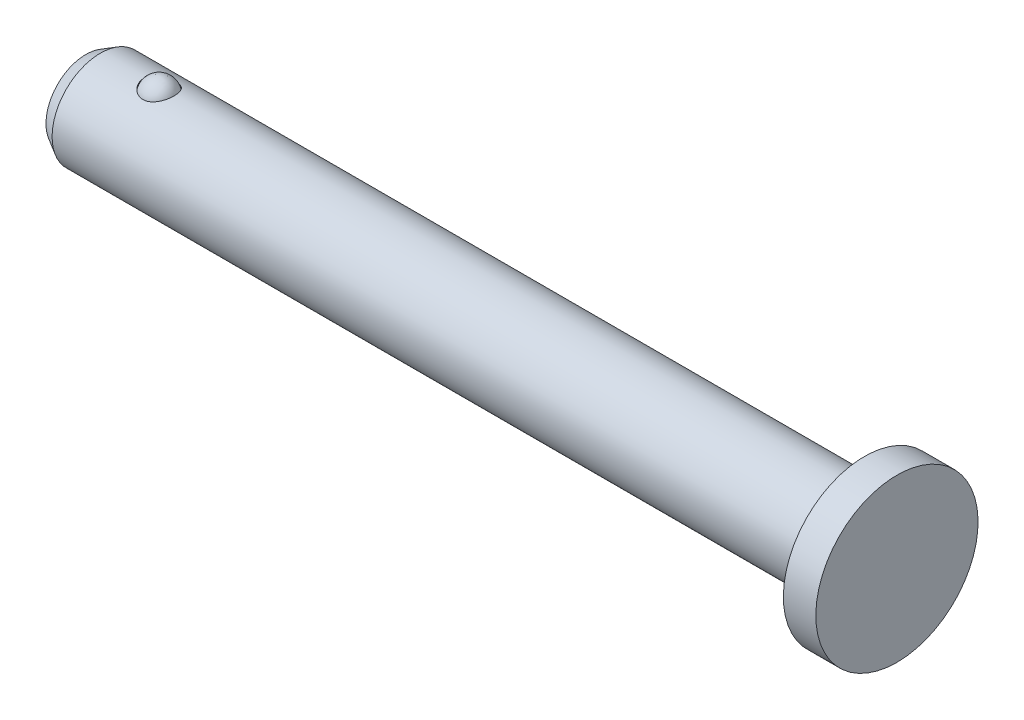
SolidWorks part; units mm, degrees
other "Imported1"
other "Imported2" parameters "D1"=138.0715, "Length"=138.0715, "Usable Length"=107.0085, "Head Height"=13.3603, "Head Diameter"=7.9375, "Diameter"=4.7244, "Shaft Length"=38.1, "Ball Height"=5.1816, "Ball Width"=2.3622, "D2"=54.5332, "F"=55.499, "D10"=11.2649, "D11"=5.3256, "D4"=6.8632, "K"=3.175, "A"=19.0119, "B"=7.112, "D"=21.59, "E"=9.525, "D3"=24.257, "H"=41.275, "D5"=24.257, "Useable Length"=25.4, "D6"=0.9873, "D7"=3.8918, "D8"=4.5254, "D9"=5.5856, "G"=64.77, "D12"=34.036, "C"=6.8932, "A1"=15, "D13"=1.6682, "J"=3.048, "D14"=90, "D15"=34.5361, "Head Dia"=9.525
ref_plane "Front" through (0, 0, 0) normal (0, 0, 1) x (1, 0, 0)
ref_plane "Top" through (0, 0, 0) normal (0, 1, 0) x (1, 0, 0)
ref_plane "Right" through (0, 0, 0) normal (1, 0, 0) x (0, 0, -1)
sketch "Sketch4" plane through (0, 0, 0) normal (0, 0, 1) x (1, 0, 0)
  line L0 (-16.2623, -2.3622) -> (-16.2623, 2.8194) construction
  line L1 (19.8438, -2.3622) -> (-19.8437, -2.3622) construction
  line L2 (19.8438, -2.3622) -> (19.8438, 2.3622) construction
  line L3 (19.8438, 2.3622) -> (-19.8437, 2.3622) construction
  line L4 (-19.8437, -2.3622) -> (-19.8437, 2.3622) construction
  line L5 (19.8438, -2.3622) -> (-19.8437, 2.3622) construction
  line L6 (19.8438, 2.3622) -> (-19.8437, -2.3622) construction
  line L7 (19.8438, 3.9687) -> (18.2563, 3.9687)
  line L8 (19.8438, 3.9687) -> (19.8438, -3.9688)
  line L9 (19.8438, -3.9688) -> (18.2563, -3.9688)
  line L10 (18.2563, 3.9687) -> (18.2563, -3.9688)
  line L11 (19.8438, 3.9687) -> (18.2563, -3.9688) construction
  line L12 (19.8438, -3.9688) -> (18.2563, 3.9687) construction
  line L13 (-15.0812, 2.3622) -> (-17.4434, 2.3622) construction
  point P0 (0, 0)
  point P6 (-15.0812, 2.3622)
  point P12 (19.05, 0)
  point P17 (-16.2623, 2.3622)
  dimension "Head Height" = 1.5875
sketch "Sketch1" plane through (0, 0, 0) normal (0, 0, 1) x (1, 0, 0)
  line L0 (19.8438, 3.9687) -> (18.2563, 3.9687)
  line L1 (18.2563, 2.3622) -> (18.2563, 3.9687)
  line L4 (19.8438, 3.9687) -> (19.8438, 0)
  line L5 (19.8438, 3.9687) -> (19.8438, -3.9688) construction
  line L6 (18.2563, 3.9687) -> (18.2563, -3.9688) construction
  line L9 (19.8438, 3.9687) -> (18.2563, 3.9687) construction
  line L13 (-19.8437, -2.3622) -> (-19.8437, 2.3622) construction
  line L16 (18.2563, 2.3622) -> (-19.1351, 2.3622)
  line L17 (-19.8437, 2.3622) -> (-19.8437, 1.9531) construction
  line L19 (-19.1351, 2.3622) -> (-19.8437, 2.3622) construction
  line L22 (-19.8437, -2.3622) -> (-19.1351, -2.3622) construction
  line L24 (-19.8437, 0) -> (19.8438, 0)
  line L26 (-16.2623, -2.3622) -> (-16.2623, 2.8194) construction
  line L27 (19.8438, -2.3622) -> (-19.8437, 2.3622) construction
  line L29 (-19.8437, 0) -> (-19.8437, -1.9531) construction
  line L36 (18.2563, 0) -> (18.2563, 2.3622) construction
  line L37 (-19.8437, 1.9531) -> (-19.8437, 0)
  line L38 (-19.1351, -2.3622) -> (19.8438, -2.3622) construction
  line L39 (-19.8437, -1.9531) -> (-19.8437, -2.3622) construction
  line L40 (-19.1351, 2.3622) -> (-19.8437, 1.9531)
  line L42 (-19.1351, -2.3622) -> (-19.8437, -1.9531) construction
  line L43 (-19.1351, 2.3622) -> (-19.1351, -2.3622) construction
  circle A0 centre (-16.2623, 2.0299) radius 0.7895 construction
  point P4 (19.8438, 1.9844)
  point P26 (-17.0519, 2.0299)
  point P35 (-16.2623, 2.3622)
  dimension "D1" = 30
  dimension "D2" = 0.7087
revolve "Revolve1" add sketch "Sketch1" angle 360 about L24
sketch "Sketch2" plane through (0, 0, 0) normal (0, 0, 1) x (1, 0, 0)
  line L0 (-15.4474, 2.0299) -> (-17.0773, 2.0299)
  line L1 (-16.2623, 2.8194) -> (-16.2623, 2.8448) construction
  line L2 (-15.4474, 2.0299) -> (-13.8175, 2.0299) construction
  circle A1 centre (-16.2623, 2.0299) radius 0.7895 construction
  arc A2 (-17.0773, 2.0299) -> (-15.4474, 2.0299) centre (-16.2623, 2.0299) cw
  circle A4 centre (-16.2623, 2.0299) radius 0.7895 construction
  dimension "D1" = 0.0254
revolve "Cut-Revolve1" cut sketch "Sketch2" angle 360 about L2
sketch "Sketch3" plane through (0, 0, 0) normal (0, 0, 1) x (1, 0, 0)
  line L0 (-15.4728, 2.0299) -> (-17.0519, 2.0299)
  line L1 (-15.4728, 2.0299) -> (-13.8937, 2.0299) construction
  arc A1 (-15.4728, 2.0299) -> (-17.0519, 2.0299) centre (-16.2623, 2.0299) ccw
  circle A2 centre (-16.2623, 2.0299) radius 0.7895 construction
  point P5 (-15.4728, 2.0299)
revolve "Revolve2" add sketch "Sketch3" angle 360 about L1
equation "\"Ball Width@Sketch4\"=\"Diameter@Sketch4\"*.5"
equation "\"D2@Sketch1\"= \"Diameter@Sketch4\" * .15"
